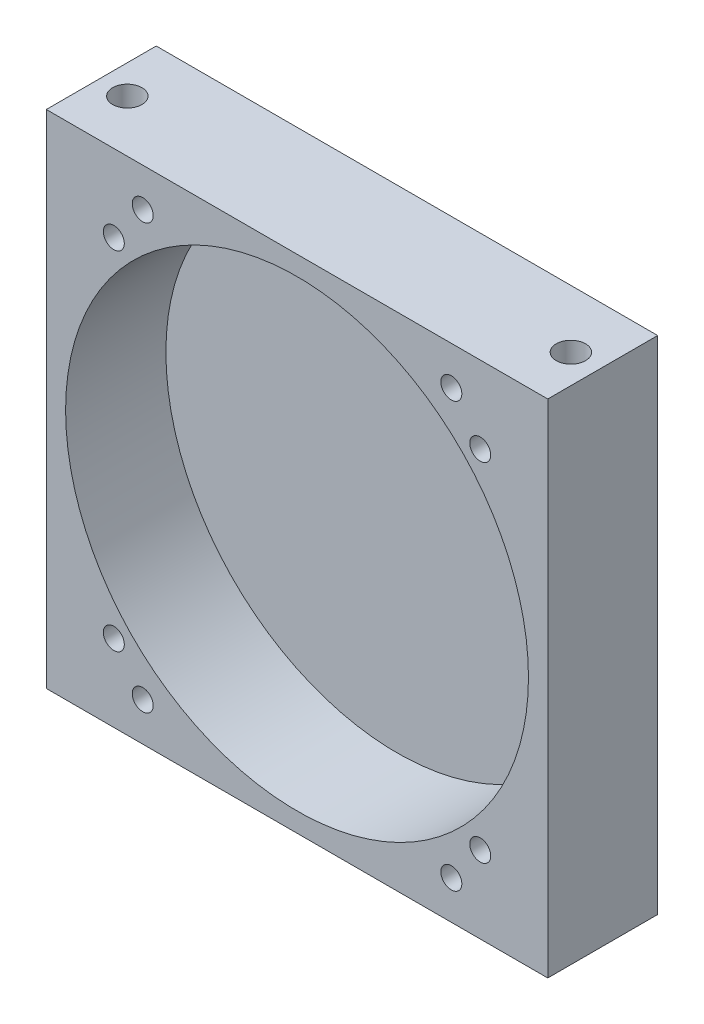
SolidWorks part; units mm, degrees
material "6061-T6 (SS)"
ref_plane "Front Plane" through (0, 0, 0) normal (0, 0, 1) x (1, 0, 0)
ref_plane "Top Plane" through (0, 0, 0) normal (0, 1, 0) x (1, 0, 0)
ref_plane "Right Plane" through (0, 0, 0) normal (1, 0, 0) x (0, 0, -1)
sketch "Sketch1" plane through (0, 0, 0) normal (0, 0, 1) x (1, 0, 0)
  line L1 (41.275, -41.275) -> (-41.275, -41.275)
  line L2 (41.275, -41.275) -> (41.275, 41.275)
  line L3 (41.275, 41.275) -> (-41.275, 41.275)
  line L4 (-41.275, -41.275) -> (-41.275, 41.275)
  line L5 (41.275, -41.275) -> (-41.275, 41.275) construction
  line L6 (41.275, 41.275) -> (-41.275, -41.275) construction
  point P0 (0, 0)
  dimension "D1" = 82.55
  dimension "D2" = 82.55
extrude "Boss-Extrude1" add sketch "Sketch1" along normal blind 18.0975
sketch "Sketch2" plane through (0, 0, 18.0975) normal (0, 0, 1) x (1, 0, 0)
  circle A0 centre (0, 0) radius 38.1
  dimension "D1" = 76.2
extrude "Cut-Extrude1" cut sketch "Sketch2" against normal blind 16.51
hole_wizard "#10-32 Tapped Hole1" positions "Sketch4" profile "Sketch3" tap size "#10-32" standard "ANSI Inch"
sketch "Sketch4" plane through (0, 41.275, 0) normal (0, 1, 0) x (-1, 0, 0)
  line L0 (-36.5125, 9.525) -> (0, 0) construction
  line L1 (0, 0) -> (36.5125, 9.525) construction
  line L3 (-41.275, 0) -> (41.275, 0) construction
  point P0 (36.5125, 9.525)
  point P1 (-36.5125, 9.525)
  dimension "D1" = 73.025
  dimension "D2" = 9.525
sketch "Sketch3" plane through (-36.5125, 41.275, 9.525) normal (1, 0, 0) x (0, 0, 1)
  line L0 (0, 0) -> (0, 20.2633)
  line L1 (0, 20.2633) -> (2.0193, 19.05)
  line L2 (2.0193, 19.05) -> (2.0193, 18.288)
  line L3 (2.0193, 18.288) -> (2.413, 18.288)
  line L4 (2.413, 18.288) -> (2.413, 0)
  line L5 (2.413, 0) -> (0, 0)
  line L10 (0, 20.2633) -> (-2.0193, 19.05) construction
  line L11 (0, -6.35) -> (0, 107.95) construction
  dimension "Tap Drill Dia." = 4.0386
  dimension "Tap Drill Depth" = 19.05
  dimension "Thread Major Dia." = 4.826
  dimension "Thread Depth" = 18.288
  dimension "Drill Angle" = 118
mirror "Mirror1" about plane through (0, 0, 0) normal (0, 1, 0) of "#10-32 Tapped Hole1"
hole_wizard "#8-32 Tapped Hole1" positions "Sketch6" profile "Sketch5" tap size "#8-32" standard "ANSI Inch"
sketch "Sketch6" plane through (0, 0, 18.0975) normal (0, 0, 1) x (1, 0, 0)
  line L0 (25.4, -34.925) -> (-25.4, 34.925) construction
  line L3 (25.4, 34.925) -> (-25.4, -34.925) construction
  point P0 (25.4, -34.925)
  point P1 (-25.4, -34.925)
  point P3 (-25.4, 34.925)
  point P5 (25.4, 34.925)
  dimension "D1" = 50.8
  dimension "D2" = 69.85
sketch "Sketch5" plane through (25.4, -34.925, 18.0975) normal (1, 0, 0) x (0, -1, 0)
  line L0 (0, 0) -> (0, 17.0398)
  line L1 (0, 17.0398) -> (1.7272, 16.002)
  line L2 (1.7272, 16.002) -> (1.7272, 0)
  line L5 (1.7272, 0) -> (0, 0)
  line L10 (0, 17.0398) -> (-1.7272, 16.002) construction
  line L11 (0, -6.35) -> (0, 107.95) construction
  dimension "Tap Drill Dia." = 3.4544
  dimension "Tap Drill Depth" = 16.002
  dimension "Drill Angle" = 118
cosmetic thread "Hole Thread1" parameters "D1"=8.382, "D2"=4.1656
cosmetic thread "Hole Thread2" parameters "D1"=8.382, "D2"=4.1656
cosmetic thread "Hole Thread3" parameters "D1"=8.382, "D2"=4.1656
cosmetic thread "Hole Thread4" parameters "D1"=8.382, "D2"=4.1656
hole_wizard "#8-32 Tapped Hole2" positions "Sketch8" profile "Sketch7" tap size "#8-32" standard "ANSI Inch"
sketch "Sketch8" plane through (0, 0, 18.0975) normal (0, 0, 1) x (1, 0, 0)
  line L1 (-30.1625, 28.575) -> (30.1625, 28.575)
  line L2 (-30.1625, 28.575) -> (-30.1625, -28.575)
  line L3 (-30.1625, -28.575) -> (30.1625, -28.575)
  line L4 (30.1625, 28.575) -> (30.1625, -28.575)
  line L5 (-30.1625, 28.575) -> (30.1625, -28.575) construction
  line L6 (-30.1625, -28.575) -> (30.1625, 28.575) construction
  point P2 (30.1625, -28.575)
  point P79 (-30.1625, 28.575)
  point P80 (-30.1625, -28.575)
  point P81 (30.1625, 28.575)
  dimension "D1" = 60.325
  dimension "D2" = 57.15
sketch "Sketch7" plane through (30.1625, -28.575, 18.0975) normal (1, 0, 0) x (0, -1, 0)
  line L0 (0, 0) -> (0, 17.0398)
  line L1 (0, 17.0398) -> (1.7272, 16.002)
  line L2 (1.7272, 16.002) -> (1.7272, 0)
  line L5 (1.7272, 0) -> (0, 0)
  line L10 (0, 17.0398) -> (-1.7272, 16.002) construction
  line L11 (0, -6.35) -> (0, 107.95) construction
  dimension "Tap Drill Dia." = 3.4544
  dimension "Tap Drill Depth" = 16.002
  dimension "Drill Angle" = 118
cosmetic thread "Hole Thread5" parameters "D1"=8.382, "D2"=4.1656
cosmetic thread "Hole Thread6" parameters "D1"=8.382, "D2"=4.1656
cosmetic thread "Hole Thread7" parameters "D1"=8.382, "D2"=4.1656
cosmetic thread "Hole Thread8" parameters "D1"=8.382, "D2"=4.1656
